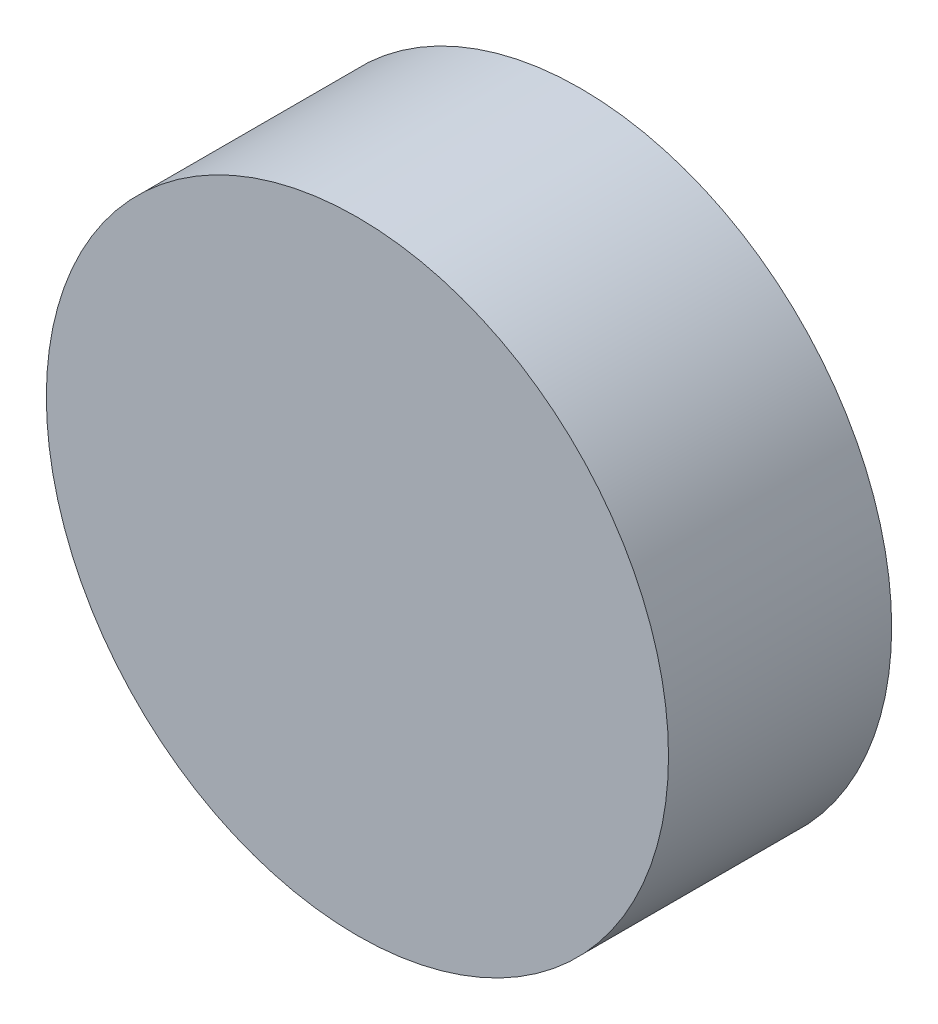
SolidWorks part; units mm, degrees
material "Boron"
ref_plane "Front" through (0, 0, 0) normal (0, 0, 1) x (1, 0, 0)
ref_plane "Top" through (0, 0, 0) normal (0, 1, 0) x (1, 0, 0)
ref_plane "Right" through (0, 0, 0) normal (1, 0, 0) x (0, 0, -1)
sketch "Sketch1" plane through (0, 0, 0) normal (0, 0, 1) x (1, 0, 0)
  circle A2 centre (0, 0) radius 75
extrude "Boss-Extrude1" add sketch "Sketch1" along normal blind 53.8 contours A2
